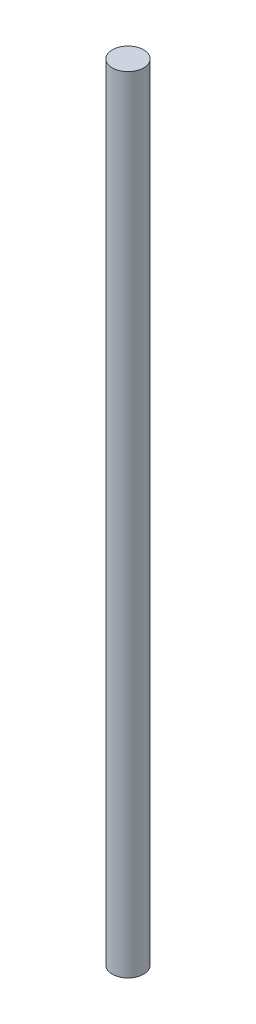
SolidWorks part; units mm, degrees
ref_plane "Front Plane" through (0, 0, 0) normal (0, 0, 1) x (1, 0, 0)
ref_plane "Top Plane" through (0, 0, 0) normal (0, 1, 0) x (1, 0, 0)
ref_plane "Right Plane" through (0, 0, 0) normal (1, 0, 0) x (0, 0, -1)
sketch "Sketch1" plane through (0, 0, 0) normal (0, 1, 0) x (1, 0, 0)
  circle A0 centre (0, 0) radius 4
  dimension "D1" = 8
extrude "Boss-Extrude1" add sketch "Sketch1" along normal blind 200
